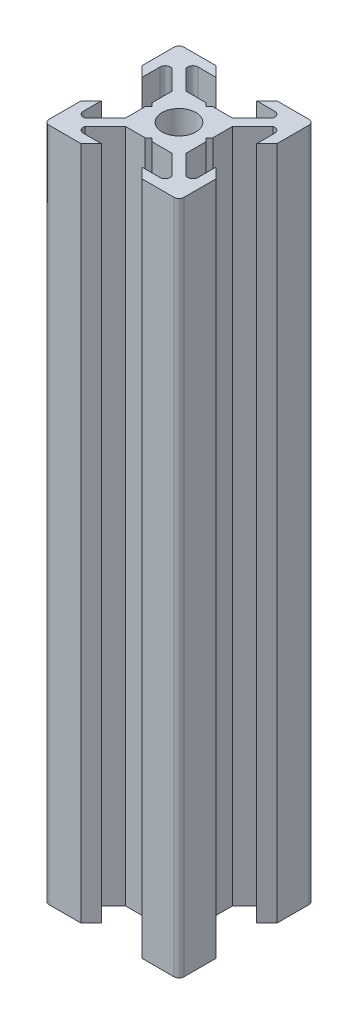
SolidWorks part; units mm, degrees
ref_plane "Face" through (0, 0, 0) normal (0, 0, 1) x (1, 0, 0)
ref_plane "Dessus" through (0, 0, 0) normal (0, 1, 0) x (1, 0, 0)
ref_plane "Droite" through (0, 0, 0) normal (1, 0, 0) x (0, 0, -1)
sketch "Esquisse1" plane through (0, 0, 0) normal (0, 1, 0) x (1, 0, 0)
  line L0 (0, 0) -> (0, 10) construction
  line L1 (0, 0) -> (-10, 0) construction
  line L2 (-10, 0) -> (-10, 10) construction
  line L3 (-10, 10) -> (0, 10) construction
  line L4 (0, 4) -> (-0.5, 4.5)
  line L5 (-0.5, 4.5) -> (-3.4393, 4.5)
  line L6 (-3.4393, 4.5) -> (-6.4393, 7.5)
  line L7 (-6.4393, 7.5) -> (-6.4393, 8.5)
  line L8 (-6.4393, 8.5) -> (-3, 8.5)
  line L9 (-3, 8.5) -> (-4.5, 10)
  line L10 (-4.5, 10) -> (-10, 10)
  line L11 (0, 0) -> (-10, 10) construction
  line L12 (-10, 4.5) -> (-10, 10)
  line L13 (-8.5, 3) -> (-10, 4.5)
  line L14 (-8.5, 6.4393) -> (-8.5, 3)
  line L15 (-7.5, 6.4393) -> (-8.5, 6.4393)
  line L16 (-4.5, 3.4393) -> (-7.5, 6.4393)
  line L17 (-4.5, 0.5) -> (-4.5, 3.4393)
  line L18 (-4, 0) -> (-4.5, 0.5)
  line L19 (0, -4) -> (-0.5, -4.5)
  line L20 (-0.5, -4.5) -> (-3.4393, -4.5)
  line L21 (-4, 0) -> (-4.5, -0.5)
  line L22 (-4.5, -0.5) -> (-4.5, -3.4393)
  line L23 (-4.5, -3.4393) -> (-7.5, -6.4393)
  line L24 (-3.4393, -4.5) -> (-6.4393, -7.5)
  line L25 (-3, -8.5) -> (-4.5, -10)
  line L26 (-6.4393, -8.5) -> (-3, -8.5)
  line L27 (-6.4393, -7.5) -> (-6.4393, -8.5)
  line L28 (-7.5, -6.4393) -> (-8.5, -6.4393)
  line L29 (-4.5, -10) -> (-10, -10)
  line L30 (-10, -4.5) -> (-10, -10)
  line L31 (-8.5, -3) -> (-10, -4.5)
  line L32 (-8.5, -6.4393) -> (-8.5, -3)
  line L33 (8.5, -6.4393) -> (8.5, -3)
  line L34 (8.5, -3) -> (10, -4.5)
  line L35 (10, -4.5) -> (10, -10)
  line L36 (4.5, -10) -> (10, -10)
  line L37 (7.5, -6.4393) -> (8.5, -6.4393)
  line L38 (6.4393, -7.5) -> (6.4393, -8.5)
  line L39 (6.4393, -8.5) -> (3, -8.5)
  line L40 (3, -8.5) -> (4.5, -10)
  line L41 (3.4393, -4.5) -> (6.4393, -7.5)
  line L42 (4.5, -3.4393) -> (7.5, -6.4393)
  line L43 (4.5, -0.5) -> (4.5, -3.4393)
  line L44 (4, 0) -> (4.5, -0.5)
  line L45 (0.5, -4.5) -> (3.4393, -4.5)
  line L46 (0, -4) -> (0.5, -4.5)
  line L47 (4, 0) -> (4.5, 0.5)
  line L48 (4.5, 0.5) -> (4.5, 3.4393)
  line L49 (4.5, 3.4393) -> (7.5, 6.4393)
  line L50 (7.5, 6.4393) -> (8.5, 6.4393)
  line L51 (8.5, 6.4393) -> (8.5, 3)
  line L52 (8.5, 3) -> (10, 4.5)
  line L53 (10, 4.5) -> (10, 10)
  line L54 (4.5, 10) -> (10, 10)
  line L55 (3, 8.5) -> (4.5, 10)
  line L56 (6.4393, 8.5) -> (3, 8.5)
  line L57 (6.4393, 7.5) -> (6.4393, 8.5)
  line L58 (3.4393, 4.5) -> (6.4393, 7.5)
  line L59 (0.5, 4.5) -> (3.4393, 4.5)
  line L60 (0, 4) -> (0.5, 4.5)
  circle A0 centre (0, 0) radius 2.5
  dimension "D10" = 5
  dimension "D1" = 10
  dimension "D2" = 45
  dimension "D3" = 45
  dimension "D4" = 1.5
  dimension "D5" = 7
  dimension "D6" = 1
  dimension "D7" = 4.5
  dimension "D8" = 0.5
  dimension "D9" = 0.75
extrude "Extrusion1" add sketch "Esquisse1" along normal blind 100
fillet "Congé1" radius 0.75 12 edges at (-8.5, 50, -6.4393) (-6.4393, 50, -8.5) (8.5, 50, -6.4393) (6.4393, 50, -8.5) (-8.5, 50, 6.4393) (-6.4393, 50, 8.5) (8.5, 50, 6.4393) (6.4393, 50, 8.5) (10, 50, -10) (-10, 50, -10) (-10, 50, 10) (10, 50, 10)
